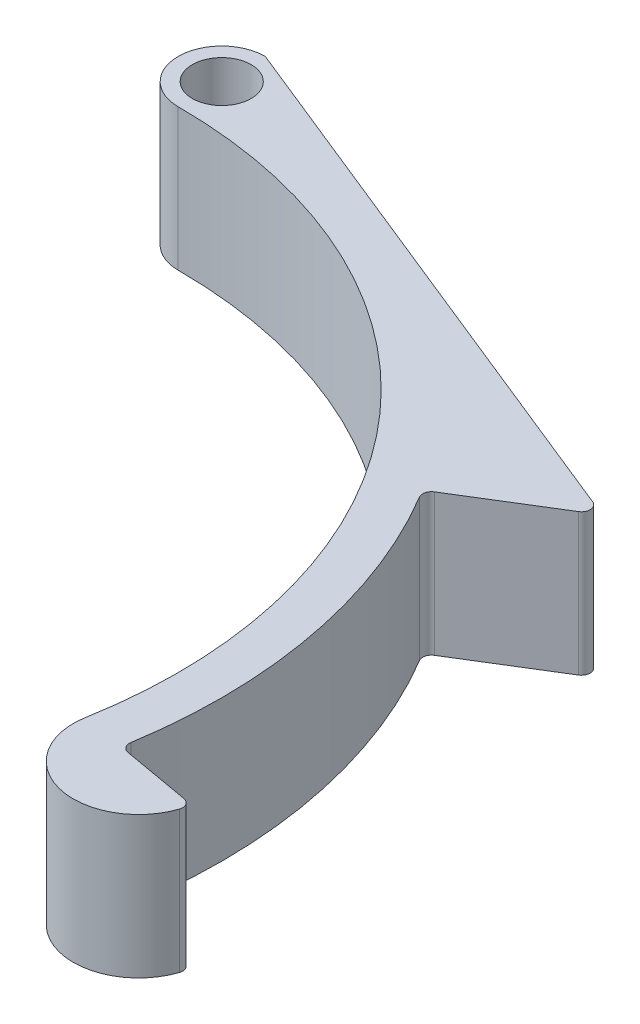
SolidWorks part; units mm, degrees
ref_plane "Front Plane" through (0, 0, 0) normal (0, 0, 1) x (1, 0, 0)
ref_plane "Top Plane" through (0, 0, 0) normal (0, 1, 0) x (1, 0, 0)
ref_plane "Right Plane" through (0, 0, 0) normal (1, 0, 0) x (0, 0, -1)
sketch "Sketch1" plane through (0, 0, 0) normal (0, 1, 0) x (1, 0, 0)
  line L0 (0, 0) -> (44.3163, -7.8142) construction
  line L1 (0, 0) -> (0, -45) construction
  line L2 (0, 0) -> (81.732, -14.4116) construction
  line L3 (0, 53) -> (51.921, 32.0189)
  line L4 (51.921, 32.0189) -> (41.707, 25.7201)
  line L5 (0, 53) -> (0, 49)
  line L7 (0, 49) -> (0, 53)
  line L8 (56.134, -9.8979) -> (48.2556, -8.5088)
  circle A0 centre (0, 0) radius 45 construction
  arc A1 (0, 45) -> (44.3163, -7.8142) centre (0, 0) cw
  arc A2 (0, 45) -> (0, 53) centre (0, 49) cw
  arc A4 (48.2556, -8.5088) -> (0, 49) centre (0, 0) ccw
  circle A5 centre (0, 49) radius 2.7
  arc A6 (41.707, 25.7201) -> (0, 49) centre (0, 0) ccw
  arc A7 (44.3163, -7.8142) -> (56.134, -9.8979) centre (50.2252, -8.8561) ccw
  dimension "D1" = 90
  dimension "D5" = 56
  dimension "D6" = 5.4
  dimension "D2" = 80
  dimension "D3" = 8
  dimension "D4" = 4
  dimension "D7" = 12
  dimension "D8" = 12
extrude "Boss-Extrude1" add sketch "Sketch1" along normal blind 13
fillet "Fillet1" radius 0.8 5 edges at (0, 6.5, -53) (51.921, 6.5, -32.0189) (41.707, 6.5, -25.7201) (56.134, 6.5, 9.8979) (48.2556, 6.5, 8.5088)
